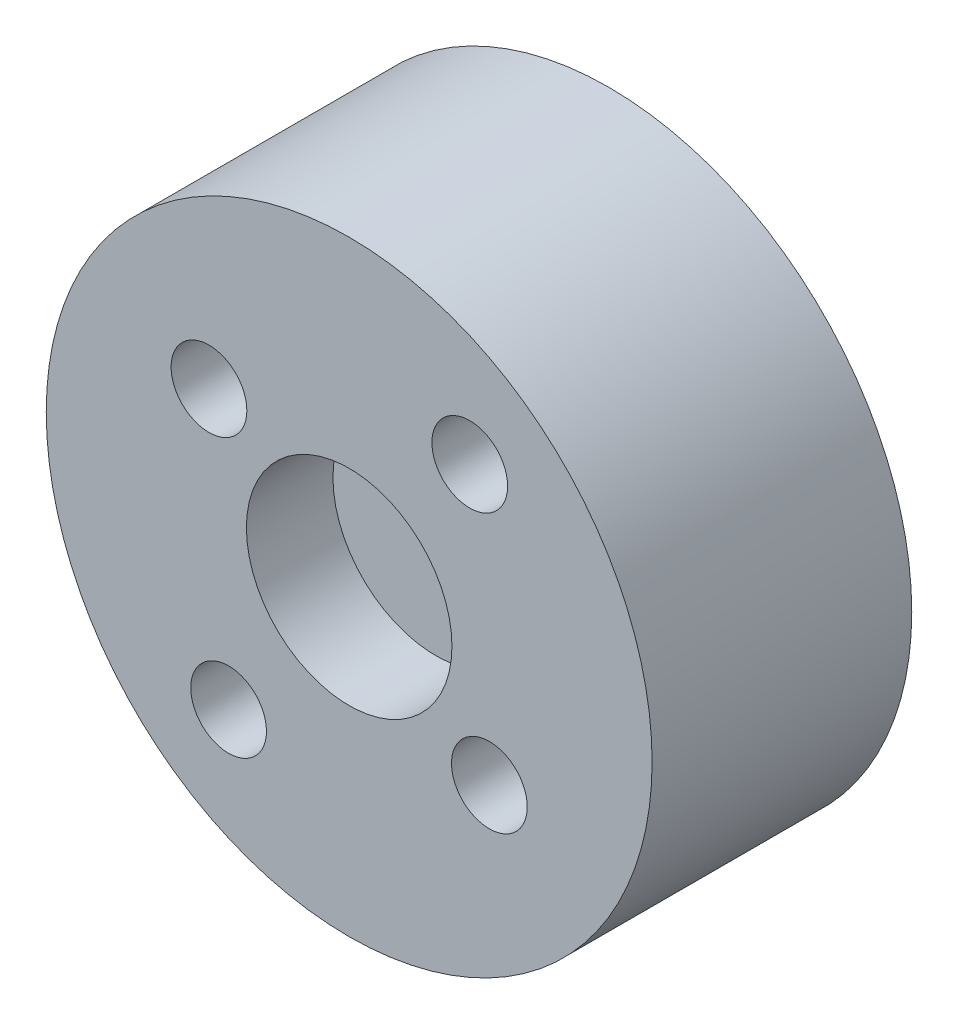
SolidWorks part; units mm, degrees
ref_plane "Front Plane" through (0, 0, 0) normal (0, 0, 1) x (1, 0, 0)
ref_plane "Top Plane" through (0, 0, 0) normal (0, 1, 0) x (1, 0, 0)
ref_plane "Right Plane" through (0, 0, 0) normal (1, 0, 0) x (0, 0, -1)
sketch "Sketch2" plane through (0, 0, 12) normal (0, 0, -1) x (-1, 0, 0)
  circle A0 centre (0, 0) radius 14
  dimension "D1" = 28
extrude "Boss-Extrude1" add sketch "Sketch2" along normal up to surface (12 mm away)
sketch "Sketch3" plane through (0, 0, 12) normal (0, 0, 1) x (1, 0, 0)
  circle A0 centre (-6.4792, 4.6925) radius 1.75
  circle A1 centre (5.5723, 7.6941) radius 1.75
  circle A2 centre (6.4792, -4.6925) radius 1.75
  circle A3 centre (-5.5723, -7.6941) radius 1.75
  dimension "D1" = 3.5
  dimension "D2" = 3.5
  dimension "D3" = 3.5
  dimension "D4" = 3.5
extrude "Cut-Extrude1" cut sketch "Sketch3" against normal through all
sketch "Sketch4" plane through (0, 0, 12) normal (0, 0, 1) x (1, 0, 0)
  circle A0 centre (0, 0) radius 4.75
  dimension "D1" = 9.5
extrude "Cut-Extrude2" cut sketch "Sketch4" against normal blind 4
